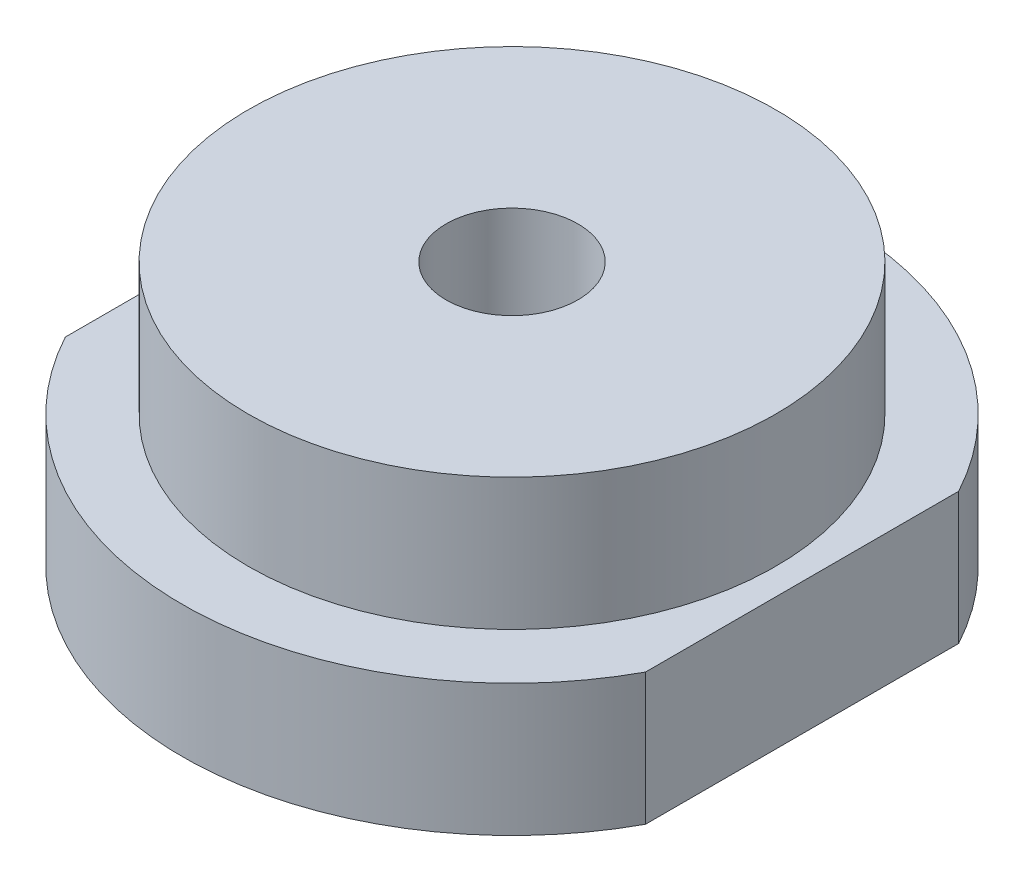
SolidWorks part; units mm, degrees
ref_plane "Ebene vorne" through (0, 0, 0) normal (0, 0, 1) x (1, 0, 0)
ref_plane "Ebene oben" through (0, 0, 0) normal (0, 1, 0) x (1, 0, 0)
ref_plane "Ebene rechts" through (0, 0, 0) normal (1, 0, 0) x (0, 0, -1)
sketch "Skizze1" plane through (0, 0, 0) normal (0, 1, 0) x (1, 0, 0)
  circle A0 centre (0, 0) radius 12.5
  dimension "D1" = 25
extrude "Aufsatz-Linear austragen1" add sketch "Skizze1" along normal blind 5
sketch "Skizze2" plane through (0, 5, 0) normal (0, 1, 0) x (1, 0, 0)
  circle A0 centre (0, 0) radius 10
  dimension "D1" = 20
extrude "Aufsatz-Linear austragen2" add sketch "Skizze2" along normal blind 5
sketch "Skizze3" plane through (0, 10, 0) normal (0, 1, 0) x (1, 0, 0)
  line L0 (-11, 5.9372) -> (-11, -5.9372)
  line L1 (0, 12.5) -> (0, 0) construction
  line L2 (11, 5.9372) -> (11, -5.9372)
  circle A0 centre (0, 0) radius 12.5 construction
  arc A2 (-11, -5.9372) -> (-11, 5.9372) centre (0, 0) cw
  arc A3 (11, -5.9372) -> (11, 5.9372) centre (0, 0) ccw
  circle A4 centre (0, 0) radius 2.5
  dimension "D2" = 5
  dimension "D1" = 22
extrude "Schnitt-Linear austragen1" cut sketch "Skizze3" against normal through all
